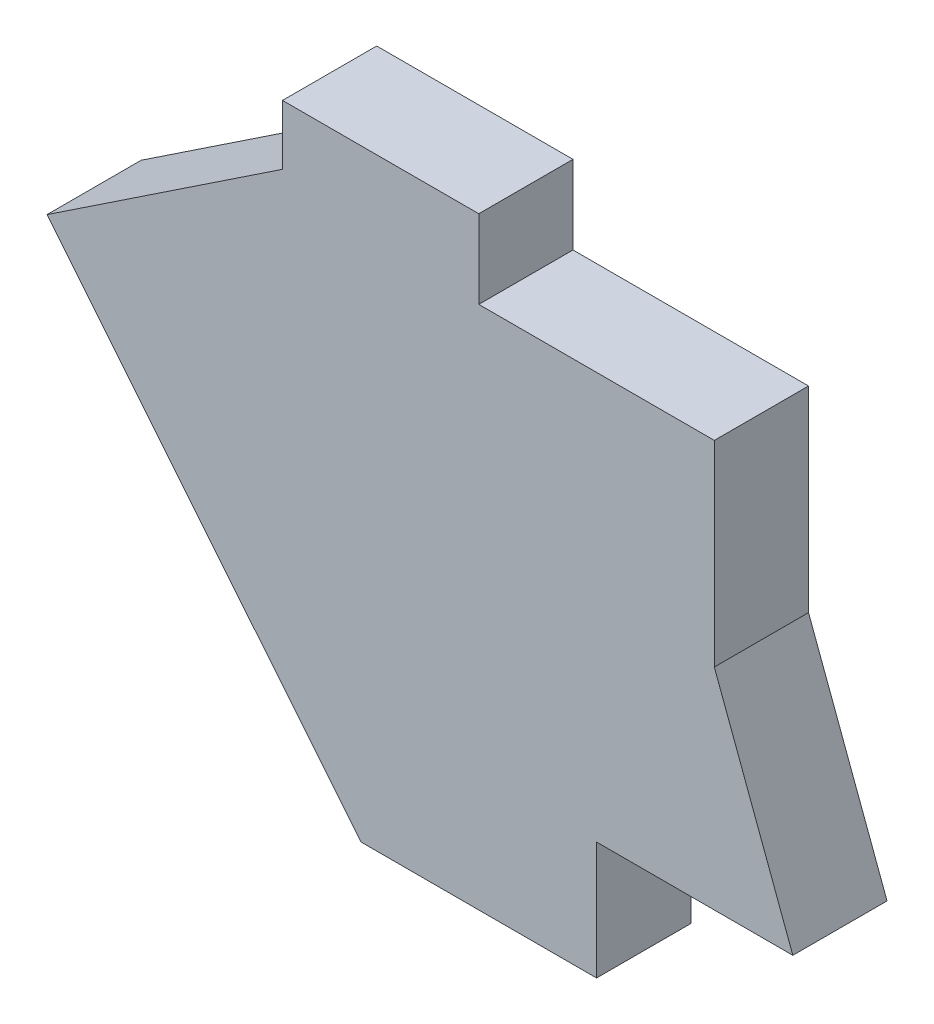
SolidWorks part; units mm, degrees
ref_plane "Front Plane" through (0, 0, 0) normal (0, 0, 1) x (1, 0, 0)
ref_plane "Top Plane" through (0, 0, 0) normal (0, 1, 0) x (1, 0, 0)
ref_plane "Right Plane" through (0, 0, 0) normal (1, 0, 0) x (0, 0, -1)
sketch "Sketch1" plane through (0, 0, 0) normal (0, 0, 1) x (1, 0, 0)
  line L0 (-19.05, -60.2652) -> (-69.85, 2.2188)
  line L1 (-69.85, 2.2188) -> (-31.75, 27.6188)
  line L2 (-31.75, 27.6188) -> (-31.75, 37.2708)
  line L3 (-31.75, 37.2708) -> (0, 37.2708)
  line L4 (0, 37.2708) -> (0, 24.5708)
  line L5 (0, 24.5708) -> (38.1, 24.5708)
  line L6 (38.1, 24.5708) -> (38.1, -7.1792)
  line L7 (38.1, -7.1792) -> (50.8, -41.2152)
  line L8 (50.8, -41.2152) -> (19.05, -41.2152)
  line L9 (19.05, -41.2152) -> (19.05, -60.2652)
  line L10 (19.05, -60.2652) -> (-19.05, -60.2652)
  point P0 (0, 0)
  point P7 (-75.8185, 2.2188)
  point P13 (-75.8185, 2.2188)
  point P15 (-75.8185, 2.2188)
  dimension "D1" = 62.484
  dimension "D2" = 120.65
  dimension "D3" = 50.8
  dimension "D4" = 38.1
  dimension "D5" = 97.536
  dimension "D6" = 9.652
  dimension "D7" = 38.1
  dimension "D8" = 38.1
  dimension "D9" = 31.75
  dimension "D10" = 19.05
  dimension "D11" = 12.7
  dimension "D12" = 12.7
extrude "Boss-Extrude1" add sketch "Sketch1" along normal blind 15.24
